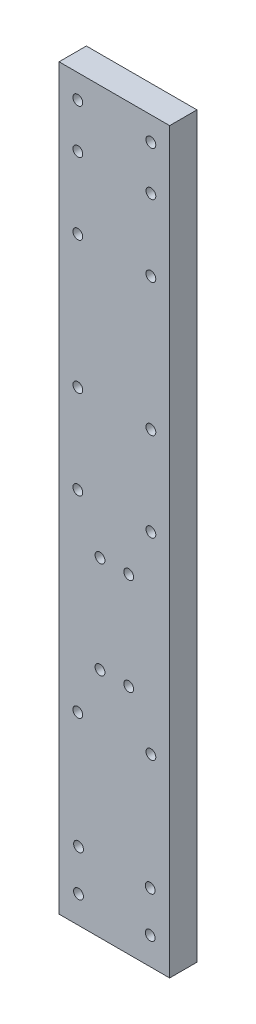
SolidWorks part; units mm, degrees
ref_plane "Front Plane" through (0, 0, 0) normal (0, 0, 1) x (1, 0, 0)
ref_plane "Top Plane" through (0, 0, 0) normal (0, 1, 0) x (1, 0, 0)
ref_plane "Right Plane" through (0, 0, 0) normal (1, 0, 0) x (0, 0, -1)
sketch "Sketch1" plane through (0, 0, 0) normal (0, 0, 1) x (1, 0, 0)
  line L0 (16.2, 0) -> (16.2, 108.14)
  line L1 (16.2, 108.14) -> (0, 108.14)
  line L2 (0, 108.14) -> (0, 0)
  line L3 (0, 0) -> (16.2, 0)
  line L4 (16.2, 57.71) -> (0, 57.71) construction
  line L5 (0, 12.5) -> (16.2, 12.5) construction
  line L6 (0, 24.5) -> (16.2, 24.5) construction
  line L7 (0, 90.16) -> (16.2, 90.16) construction
  line L8 (0, 65.71) -> (16.2, 65.71) construction
  line L9 (8.1, 108.14) -> (8.1, 96.16) construction
  line L11 (0, 96.16) -> (16.2, 96.16) construction
  circle A0 centre (13.45, 55.21) radius 0.72
  circle A1 centre (10.2, 48.21) radius 0.72
  circle A2 centre (13.45, 104.66) radius 0.72
  circle A3 centre (2.75, 98.16) radius 0.72
  circle A4 centre (6, 48.21) radius 0.72
  circle A5 centre (2.75, 27) radius 0.72
  circle A6 centre (2.75, 87.66) radius 0.72
  circle A7 centre (2.75, 55.21) radius 0.72
  circle A8 centre (13.45, 87.66) radius 0.72
  circle A9 centre (13.45, 98.16) radius 0.72
  circle A28 centre (13.45, 68.21) radius 0.72
  circle A29 centre (6, 34) radius 0.72
  circle A32 centre (2.75, 104.66) radius 0.72
  circle A33 centre (10.2, 34) radius 0.72
  circle A34 centre (2.75, 68.21) radius 0.72
  circle A35 centre (13.45, 27) radius 0.72
  circle A36 centre (2.85, 10) radius 0.72
  circle A37 centre (13.35, 10) radius 0.72
  circle A38 centre (13.35, 4) radius 0.72
  circle A39 centre (2.85, 4) radius 0.72
  dimension "D1" = 4
  dimension "D45" = 1.44
  dimension "D2" = 4
  dimension "D3" = 2.85
  dimension "D4" = 2.85
  dimension "D5" = 16.2
  dimension "D6" = 6
  dimension "D7" = 6
  dimension "D8" = 2.85
  dimension "D9" = 2.85
  dimension "D10" = 2.5
  dimension "D11" = 12
  dimension "D12" = 33.21
  dimension "D13" = 2.5
  dimension "D14" = 2.5
  dimension "D15" = 2.75
  dimension "D16" = 2.75
  dimension "D17" = 2.5
  dimension "D18" = 2.5
  dimension "D19" = 2.75
  dimension "D20" = 2.75
  dimension "D21" = 9.5
  dimension "D22" = 6
  dimension "D23" = 9.5
  dimension "D24" = 6
  dimension "D25" = 9.5
  dimension "D26" = 9.5
  dimension "D27" = 6
  dimension "D28" = 6
  dimension "D29" = 8
  dimension "D30" = 24.45
  dimension "D31" = 2.5
  dimension "D32" = 2.5
  dimension "D33" = 2.75
  dimension "D34" = 2.75
  dimension "D35" = 6
  dimension "D36" = 2.75
  dimension "D37" = 2
  dimension "D38" = 2.75
  dimension "D39" = 8.5
  dimension "D40" = 11.98
  dimension "D41" = 2.5
  dimension "D42" = 2.5
  dimension "D43" = 2.75
  dimension "D44" = 2.75
extrude "Boss-Extrude1" add sketch "Sketch1" along normal blind 4
equation "\"D12@Sketch1\"= \"HL@parametersSketch@prostheticParameters.SLDPRT\" * 0.266 - 12 - 4 'Middle PIP Length"
equation "\"D30@Sketch1\"= \"HL@parametersSketch@prostheticParameters.SLDPRT\" * 0.17 - 4 - 3'Middle MIP Length"
equation "\"D5@Sketch1\"= \"fingerWidth@parametersSketch@prostheticParameters.SLDPRT\" 'Middle Width"
equation "\"D40@Sketch1\"= \"HL@parametersSketch@prostheticParameters.SLDPRT\" * 0.108 - 3 - 5'Middle DIP Length"
equation "\"D45@Sketch1\"= 1.04 + \"tol1@parametersSketch@prostheticParameters.SLDPRT\""
